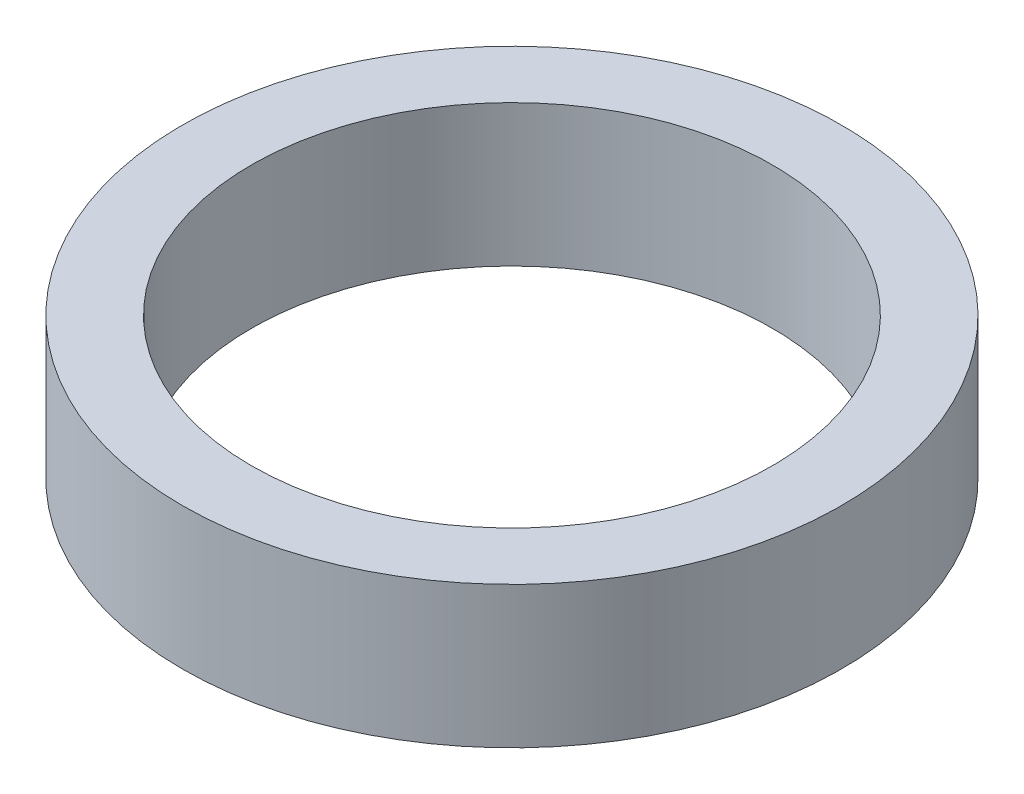
SolidWorks part; units mm, degrees
ref_plane "Front Plane" through (0, 0, 0) normal (0, 0, 1) x (1, 0, 0)
ref_plane "Top Plane" through (0, 0, 0) normal (0, 1, 0) x (1, 0, 0)
ref_plane "Right Plane" through (0, 0, 0) normal (1, 0, 0) x (0, 0, -1)
sketch "Sketch1" plane through (0, 0, 0) normal (0, 0, 1) x (1, 0, 0)
  line L0 (0, 21.4065) -> (0, -16.0932) construction
  line L1 (-51.6347, 0) -> (0, 0) construction
  line L3 (-27.0512, -7.3483) -> (-34.218, -7.3483)
  line L4 (-27.0512, -7.3483) -> (-27.0512, 7.3483)
  line L5 (-27.0512, 7.3483) -> (-34.218, 7.3483)
  line L6 (-34.218, -7.3483) -> (-34.218, 7.3483)
  line L7 (-27.0512, -7.3483) -> (-34.218, 7.3483) construction
  line L8 (-27.0512, 7.3483) -> (-34.218, -7.3483) construction
  point P5 (-30.6346, 0)
revolve "Revolve1" add sketch "Sketch1" angle 360 about L0
